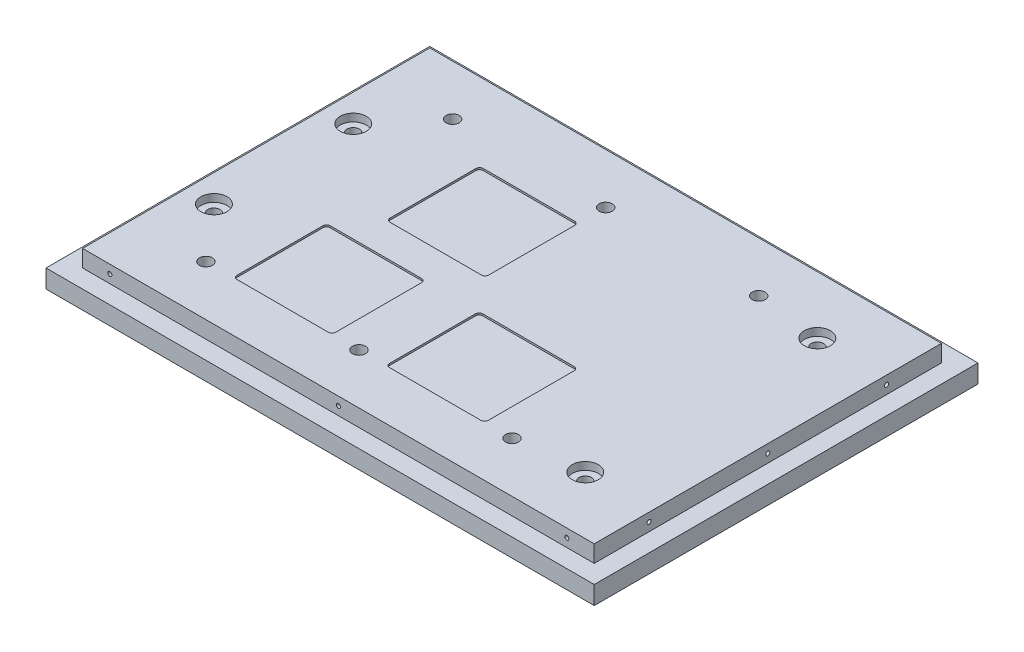
SolidWorks part; units mm, degrees
ref_plane "Front Plane" through (0, 0, 0) normal (0, 0, 1) x (1, 0, 0)
ref_plane "Top Plane" through (0, 0, 0) normal (0, 1, 0) x (1, 0, 0)
ref_plane "Right Plane" through (0, 0, 0) normal (1, 0, 0) x (0, 0, -1)
sketch "Sketch1" plane through (0, 0, 0) normal (0, 1, 0) x (1, 0, 0)
  line L1 (-172.8643, 102.5126) -> (127.1357, 102.5126)
  line L2 (-172.8643, 102.5126) -> (-172.8643, -107.4874)
  line L3 (-172.8643, -107.4874) -> (127.1357, -107.4874)
  line L4 (127.1357, 102.5126) -> (127.1357, -107.4874)
  dimension "D1" = 210
  dimension "D2" = 300
extrude "Boss-Extrude1" add sketch "Sketch1" along normal blind 10
sketch "Sketch2" plane through (0, 10, 0) normal (0, 1, 0) x (1, 0, 0)
  line L0 (-172.8643, 102.5126) -> (-172.8643, -107.4874) construction
  line L1 (-162.8643, 92.5126) -> (117.1357, 92.5126)
  line L2 (-162.8643, 92.5126) -> (-162.8643, -97.4874)
  line L3 (-162.8643, -97.4874) -> (117.1357, -97.4874)
  line L4 (117.1357, 92.5126) -> (117.1357, -97.4874)
  line L5 (127.1357, 102.5126) -> (-172.8643, 102.5126) construction
  line L6 (-172.8643, -107.4874) -> (127.1357, -107.4874) construction
  line L7 (127.1357, -107.4874) -> (127.1357, 102.5126) construction
  dimension "D1" = 10
  dimension "D2" = 10
  dimension "D3" = 10
  dimension "D4" = 10
extrude "Boss-Extrude2" add sketch "Sketch2" along normal blind 9.28
sketch "Sketch3" plane through (0, 19.28, 0) normal (0, 1, 0) x (1, 0, 0)
  line L0 (-162.8643, 92.5126) -> (-162.8643, -97.4874) construction
  line L1 (-122.8643, 65.0126) -> (44.6357, 65.0126)
  line L2 (-122.8643, 65.0126) -> (-122.8643, -69.9874)
  line L3 (-122.8643, -69.9874) -> (44.6357, -69.9874)
  line L4 (44.6357, 65.0126) -> (44.6357, -69.9874)
  line L5 (-39.1143, 65.0126) -> (-39.1143, -69.9874)
  line L6 (-122.8643, -2.4874) -> (44.6357, -2.4874)
  line L8 (-115.3772, -23.5809) -> (-65.3772, -23.5809)
  line L9 (-115.3772, -23.5809) -> (-115.3772, 26.4191)
  line L10 (-115.3772, 26.4191) -> (-65.3772, 26.4191)
  line L11 (-65.3772, -23.5809) -> (-65.3772, 26.4191)
  line L12 (-18.206, 15.3076) -> (31.794, 15.3076)
  line L13 (-18.206, 15.3076) -> (-18.206, 65.3076)
  line L14 (-18.206, 65.3076) -> (31.794, 65.3076)
  line L15 (31.794, 15.3076) -> (31.794, 65.3076)
  circle A0 centre (-122.8643, 65.0126) radius 3.57
  circle A1 centre (-39.1143, 65.0126) radius 3.57
  circle A2 centre (44.6357, 65.0126) radius 3.57
  circle A3 centre (44.6357, -69.9874) radius 3.57
  circle A4 centre (-39.1143, -69.9874) radius 3.57
  circle A5 centre (-122.8643, -69.9874) radius 3.57
  point P4 (-122.8643, -2.4874)
  point P7 (-162.8643, -2.4874)
  dimension "D5" = 7.14
  dimension "D6" = 7.14
  dimension "D1" = 167.5
  dimension "D2" = 135
  dimension "D3" = 0
  dimension "D4" = 40
  dimension "D7" = 50
  dimension "D8" = 50
  dimension "D9" = 50
  dimension "D10" = 50
extrude "1/4-20 clearance holes" cut sketch "Sketch3" against normal up to next contours A0 | A1 | A2 | A3 | A4 | A5
sketch "Sketch4" plane through (0, 0, 0) normal (0, -1, 0) x (1, 0, 0)
  line L0 (-39.1143, 69.9874) -> (-39.1143, -65.0126)
  line L1 (-122.8643, 69.9874) -> (44.6357, 69.9874)
  line L2 (-122.8643, 69.9874) -> (-122.8643, -65.0126)
  line L3 (-122.8643, -65.0126) -> (44.6357, -65.0126)
  line L4 (44.6357, 69.9874) -> (44.6357, -65.0126)
  line L5 (-122.8643, 2.4874) -> (44.6357, 2.4874)
  circle A0 centre (-122.8643, 69.9874) radius 7.5
  circle A1 centre (-39.1143, 69.9874) radius 7.5
  circle A2 centre (44.6357, 69.9874) radius 7.5
  circle A3 centre (44.6357, -65.0126) radius 7.5
  circle A4 centre (-39.1143, -65.0126) radius 7.5
  circle A5 centre (-122.8643, -65.0126) radius 7.5
  dimension "D1" = 15
  dimension "D2" = 15
extrude "Cut-Extrude2" cut sketch "Sketch4" against normal blind 10 contours A0 | A5 | A4 | A3 | A2 | A1
sketch "Sketch5" plane through (0, 0, 97.4874) normal (0, 0, 1) x (1, 0, 0)
  line L0 (-162.8643, 14.64) -> (117.1357, 14.64)
  line L1 (-162.8643, 19.28) -> (-162.8643, 10) construction
  line L2 (117.1357, 19.28) -> (117.1357, 10) construction
  line L3 (-162.8643, 19.28) -> (117.1357, 19.28) construction
  line L4 (-172.8643, 10) -> (127.1357, 10) construction
  line L5 (-22.8643, 10) -> (-22.8643, 19.28)
  circle A0 centre (-147.8643, 14.64) radius 1.13
  circle A1 centre (-22.8643, 14.64) radius 1.13
  circle A2 centre (102.1357, 14.64) radius 1.13
  dimension "D2" = 2.26
  dimension "D3" = 2.26
  dimension "D1" = 15
sketch "Sketch6" plane through (0, 0, -92.5126) normal (0, 0, -1) x (-1, 0, 0)
  line L0 (-117.1357, 14.64) -> (162.8643, 14.64)
  line L1 (-117.1357, 19.28) -> (-117.1357, 10) construction
  line L2 (162.8643, 19.28) -> (162.8643, 10) construction
  line L3 (22.8643, 19.28) -> (22.8643, 10)
  line L4 (-117.1357, 19.28) -> (162.8643, 19.28) construction
  line L5 (-127.1357, 10) -> (172.8643, 10) construction
  line L6 (-117.1357, 10) -> (162.8643, 10) construction
  circle A0 centre (-102.1357, 14.64) radius 1.13
  circle A1 centre (22.8643, 14.64) radius 1.13
  circle A2 centre (147.8643, 14.64) radius 1.13
  dimension "D2" = 2.26
  dimension "D3" = 2.26
  dimension "D1" = 15
  dimension "D4" = 250
  dimension "D5" = 4.64
sketch "Sketch7" plane through (-162.8643, 0, 0) normal (-1, 0, 0) x (0, 0, 1)
  line L0 (-92.5126, 14.64) -> (97.4874, 14.64)
  line L1 (-92.5126, 19.28) -> (-92.5126, 10) construction
  line L2 (97.4874, 19.28) -> (97.4874, 10) construction
  line L3 (2.4874, 19.28) -> (2.4874, 10)
  line L4 (-92.5126, 19.28) -> (97.4874, 19.28) construction
  line L5 (-92.5126, 10) -> (97.4874, 10) construction
  circle A0 centre (-62.5126, 14.64) radius 1.13
  circle A1 centre (2.4874, 14.64) radius 1.13
  circle A2 centre (67.4874, 14.64) radius 1.13
  dimension "D1" = 2.26
  dimension "D2" = 2.26
  dimension "D3" = 130
sketch "Sketch8" plane through (117.1357, 0, 0) normal (1, 0, 0) x (0, 0, -1)
  line L0 (-97.4874, 14.64) -> (92.5126, 14.64)
  line L1 (-97.4874, 19.28) -> (-97.4874, 10) construction
  line L2 (92.5126, 19.28) -> (92.5126, 10) construction
  line L4 (-97.4874, 19.28) -> (92.5126, 19.28) construction
  line L5 (-2.4874, 19.28) -> (-2.4874, 10)
  line L6 (-107.4874, 10) -> (102.5126, 10) construction
  circle A0 centre (-67.4874, 14.64) radius 1.13
  circle A1 centre (-2.4874, 14.64) radius 1.13
  circle A2 centre (62.5126, 14.64) radius 1.13
  dimension "D1" = 2.26
  dimension "D3" = 2.26
  dimension "D2" = 130
sketch "Sketch11" plane through (0, 19.28, 0) normal (0, 1, 0) x (1, 0, 0)
  line L1 (-122.8643, 65.0126) -> (44.6357, 65.0126)
  line L2 (-122.8643, 65.0126) -> (-122.8643, -69.9874)
  line L3 (-122.8643, -69.9874) -> (44.6357, -69.9874)
  line L4 (44.6357, 65.0126) -> (44.6357, -69.9874)
  line L5 (-107.8643, -69.9874) -> (-53.8643, -69.9874)
  line L6 (-107.8643, -69.9874) -> (-107.8643, -18.9874)
  line L7 (-107.8643, -18.9874) -> (-53.8643, -18.9874)
  line L8 (-53.8643, -69.9874) -> (-53.8643, -18.9874)
  line L9 (-24.3643, -69.9874) -> (29.6357, -69.9874)
  line L10 (-24.3643, -69.9874) -> (-24.3643, -18.9874)
  line L11 (-24.3643, -18.9874) -> (29.6357, -18.9874)
  line L12 (29.6357, -69.9874) -> (29.6357, -18.9874)
  line L13 (-93.1143, 50.0126) -> (-39.1143, 50.0126)
  line L14 (-93.1143, 50.0126) -> (-93.1143, -0.9874)
  line L15 (-93.1143, -0.9874) -> (-39.1143, -0.9874)
  line L16 (-39.1143, 50.0126) -> (-39.1143, -0.9874)
  dimension "D1" = 51
  dimension "D2" = 15
  dimension "D3" = 54
  dimension "D4" = 54
  dimension "D5" = 54
  dimension "D6" = 15
  dimension "D7" = 15
  dimension "D8" = 51
  dimension "D9" = 51
  dimension "D10" = 29.75
extrude "TEC" cut sketch "Sketch11" against normal blind 1 contours L16 L13 L14 L15 | L3 L8 L7 L6 | L3 L12 L11 L10
fillet "Fillet1" radius 2 12 edges at (-39.1143, 18.78, -50.0126) (-93.1143, 18.78, -50.0126) (-93.1143, 18.78, 0.9874) (-39.1143, 18.78, 0.9874) (29.6357, 18.78, 18.9874) (29.6357, 18.78, 69.9874) (-24.3643, 18.78, 18.9874) (-24.3643, 18.78, 69.9874) (-107.8643, 18.78, 69.9874) (-53.8643, 18.78, 69.9874) (-53.8643, 18.78, 18.9874) (-107.8643, 18.78, 18.9874)
sketch "Sketch12" plane through (0, 19.28, 0) normal (0, 1, 0) x (1, 0, 0)
  line L0 (-162.8643, 92.5126) -> (-162.8643, -97.4874) construction
  line L1 (-147.8643, 61.0126) -> (80.7357, 61.0126)
  line L2 (-147.8643, 61.0126) -> (-147.8643, -65.9874)
  line L3 (-147.8643, -65.9874) -> (80.7357, -65.9874)
  line L4 (80.7357, 61.0126) -> (80.7357, -65.9874)
  point P6 (-147.8643, -2.4874)
  point P7 (-162.8643, -2.4874)
  point P8 (-147.8643, 35.6126)
  point P9 (-147.8643, -40.5874)
  dimension "D1" = 228.6
  dimension "D2" = 15
  dimension "D3" = 0
  dimension "D4" = 127
  dimension "D5" = 25.4
  dimension "D6" = 25.4
hole_wizard "#4-40 Tapped Hole1" positions "Sketch15" profile "Sketch16" tap size "#4-40" standard "ANSI Inch"
sketch "Sketch15" plane through (-162.8643, 0, 0) normal (-1, 0, 0) x (0, 0, 1)
  point P0 (-62.5126, 14.64)
  point P3 (2.4874, 14.64)
  point P6 (67.4874, 14.64)
cosmetic thread "Hole Thread1" parameters "D1"=10, "D2"=2.8448
cosmetic thread "Hole Thread2" parameters "D1"=10, "D2"=2.8448
cosmetic thread "Hole Thread3" parameters "D1"=10, "D2"=2.8448
sketch "Sketch16" plane through (-162.8643, 14.64, -62.5126) normal (0, 1, 0) x (0, 0, 1)
  line L0 (0, 0) -> (0, 13.6792)
  line L1 (0, 13.6792) -> (1.1303, 13)
  line L2 (1.1303, 13) -> (1.1303, 0)
  line L5 (1.1303, 0) -> (0, 0)
  line L10 (0, 13.6792) -> (-1.1303, 13) construction
  line L11 (0, -6.35) -> (0, 107.95) construction
  dimension "Tap Drill Dia." = 2.2606
  dimension "Tap Drill Depth" = 13
  dimension "Drill Angle" = 118
hole_wizard "#4-40 Tapped Hole2" positions "Sketch17" profile "Sketch18" tap size "#4-40" standard "ANSI Inch"
sketch "Sketch17" plane through (0, 0, 97.4874) normal (0, 0, 1) x (1, 0, 0)
  point P0 (-147.8643, 14.64)
  point P3 (-22.8643, 14.64)
  point P6 (102.1357, 14.64)
sketch "Sketch18" plane through (-147.8643, 14.64, 97.4874) normal (1, 0, 0) x (0, -1, 0)
  line L0 (0, 0) -> (0, 13.6792)
  line L1 (0, 13.6792) -> (1.1303, 13)
  line L2 (1.1303, 13) -> (1.1303, 0)
  line L5 (1.1303, 0) -> (0, 0)
  line L10 (0, 13.6792) -> (-1.1303, 13) construction
  line L11 (0, -6.35) -> (0, 107.95) construction
  dimension "Tap Drill Dia." = 2.2606
  dimension "Tap Drill Depth" = 13
  dimension "Drill Angle" = 118
cosmetic thread "Hole Thread4" parameters "D1"=10, "D2"=2.8448
cosmetic thread "Hole Thread5" parameters "D1"=10, "D2"=2.8448
cosmetic thread "Hole Thread6" parameters "D1"=10, "D2"=2.8448
hole_wizard "#4-40 Tapped Hole3" positions "Sketch21" profile "Sketch22" tap size "#4-40" standard "ANSI Inch"
sketch "Sketch21" plane through (117.1357, 0, 0) normal (1, 0, 0) x (0, 0, -1)
  point P0 (-67.4874, 14.64)
  point P3 (-2.4874, 14.64)
  point P6 (62.5126, 14.64)
sketch "Sketch22" plane through (117.1357, 14.64, 67.4874) normal (0, 1, 0) x (0, 0, -1)
  line L0 (0, 0) -> (0, 13.6792)
  line L1 (0, 13.6792) -> (1.1303, 13)
  line L2 (1.1303, 13) -> (1.1303, 0)
  line L5 (1.1303, 0) -> (0, 0)
  line L10 (0, 13.6792) -> (-1.1303, 13) construction
  line L11 (0, -6.35) -> (0, 107.95) construction
  dimension "Tap Drill Dia." = 2.2606
  dimension "Tap Drill Depth" = 13
  dimension "Drill Angle" = 118
cosmetic thread "Hole Thread8" parameters "D1"=10, "D2"=2.8448
cosmetic thread "Hole Thread9" parameters "D1"=10, "D2"=2.8448
cosmetic thread "Hole Thread10" parameters "D1"=10, "D2"=2.8448
hole_wizard "#4-40 Tapped Hole4" positions "Sketch23" profile "Sketch24" tap size "#4-40" standard "ANSI Inch"
sketch "Sketch23" plane through (0, 0, -92.5126) normal (0, 0, -1) x (-1, 0, 0)
  point P0 (-102.1357, 14.64)
  point P3 (22.8643, 14.64)
  point P6 (147.8643, 14.64)
sketch "Sketch24" plane through (102.1357, 14.64, -92.5126) normal (1, 0, 0) x (0, 1, 0)
  line L0 (0, 0) -> (0, 13.6792)
  line L1 (0, 13.6792) -> (1.1303, 13)
  line L2 (1.1303, 13) -> (1.1303, 0)
  line L5 (1.1303, 0) -> (0, 0)
  line L10 (0, 13.6792) -> (-1.1303, 13) construction
  line L11 (0, -6.35) -> (0, 107.95) construction
  dimension "Tap Drill Dia." = 2.2606
  dimension "Tap Drill Depth" = 13
  dimension "Drill Angle" = 118
cosmetic thread "Hole Thread11" parameters "D1"=10, "D2"=2.8448
cosmetic thread "Hole Thread12" parameters "D1"=10, "D2"=2.8448
cosmetic thread "Hole Thread13" parameters "D1"=10, "D2"=2.8448
hole_wizard "CBORE for 1/4 Binding Head Machine Screw1" positions "Sketch25" profile "Sketch26" counterbore size "1/4" standard "ANSI Inch" end condition through all
sketch "Sketch25" plane through (0, 19.28, 0) normal (0, 1, 0) x (1, 0, 0)
  point P0 (80.7357, 61.0126)
  point P3 (80.7357, -65.9874)
  point P6 (-147.8643, 35.6126)
  point P9 (-147.8643, -40.5874)
sketch "Sketch26" plane through (80.7357, 19.28, -61.0126) normal (1, 0, 0) x (0, 0, 1)
  line L0 (0, 0) -> (0, 19.28)
  line L1 (0, 19.28) -> (3.3782, 19.28)
  line L3 (3.3782, 19.28) -> (3.3782, 4.191)
  line L4 (3.3782, 4.191) -> (7.1437, 4.191)
  line L5 (7.1437, 4.191) -> (7.1437, 0)
  line L7 (7.1437, 0) -> (0, 0)
  line L11 (0, -6.35) -> (0, 107.95) construction
  dimension "Thru Hole Dia." = 6.7564
  dimension "Thru Hole Depth" = 19.28
  dimension "C'Bore Dia." = 14.2875
  dimension "C'Bore Depth" = 4.191
